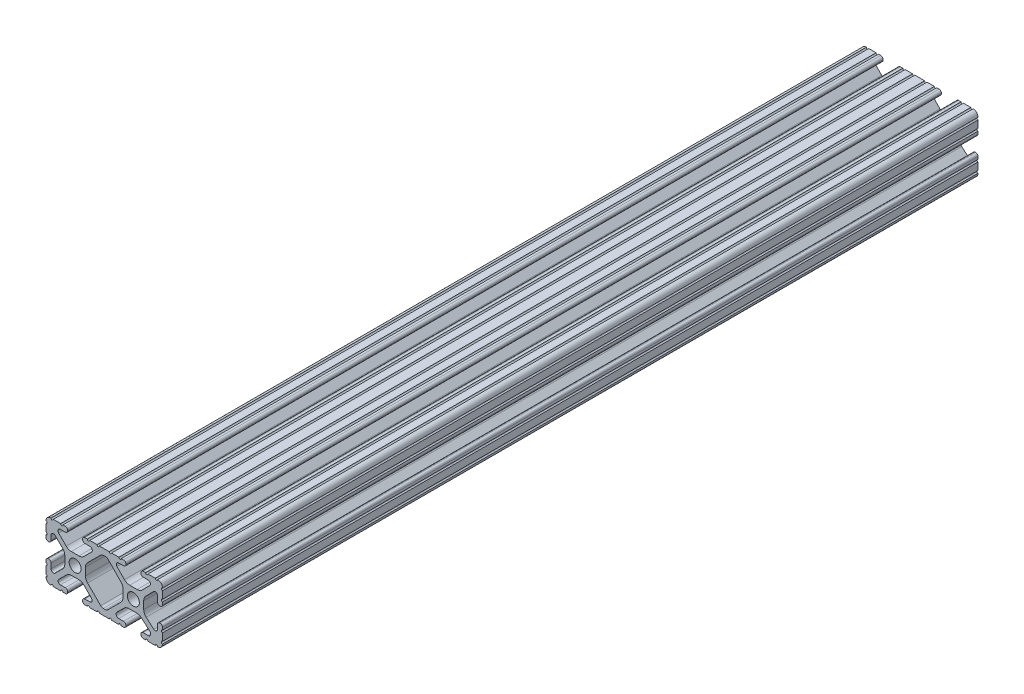
SolidWorks part; units mm, degrees
ref_plane "Front Plane" through (0, 0, 0) normal (0, 0, 1) x (1, 0, 0)
ref_plane "Top Plane" through (0, 0, 0) normal (0, 1, 0) x (1, 0, 0)
ref_plane "Right Plane" through (0, 0, 0) normal (1, 0, 0) x (0, 0, -1)
sketch "Sketch1" plane through (0, 0, 0) normal (0, 0, 1) x (1, 0, 0)
  line L0 (-7.2595, -3.8694) -> (-1.5457, -9.5728)
  line L1 (-8.1915, 1.6223) -> (-8.1915, -1.6223)
  line L2 (-1.504, 9.5765) -> (-7.252, 3.8768)
  line L3 (0.5515, 10.033) -> (-0.3952, 10.033)
  line L4 (7.2829, 3.8459) -> (1.6756, 9.5611)
  line L5 (8.1915, -1.6223) -> (8.1915, 1.6223)
  line L6 (1.5457, -9.5728) -> (7.2595, -3.8694)
  line L7 (-0.4332, -10.033) -> (0.4332, -10.033)
  line L8 (18.0171, 12.7) -> (16.9875, 12.7)
  line L9 (15.9385, 11.651) -> (15.9385, 11.5392)
  line L10 (16.9875, 10.4902) -> (19.1164, 10.4902)
  line L11 (19.8441, 8.7652) -> (16.619, 5.4551)
  line L12 (14.3449, 4.4958) -> (11.0833, 4.4958)
  line L13 (8.817, 5.4472) -> (5.5642, 8.7627)
  line L14 (6.2894, 10.4902) -> (8.4125, 10.4902)
  line L15 (9.4615, 11.5392) -> (9.4615, 11.651)
  line L16 (8.4125, 12.7) -> (7.3829, 12.7)
  line L17 (6.3669, 12.7) -> (3.1496, 12.7)
  line L18 (2.1336, 12.7) -> (-2.1336, 12.7)
  line L19 (-3.1496, 12.7) -> (-6.3669, 12.7)
  line L20 (-7.3829, 12.7) -> (-8.4125, 12.7)
  line L21 (-9.4615, 11.651) -> (-9.4615, 11.5392)
  line L22 (-8.4125, 10.4902) -> (-6.2836, 10.4902)
  line L23 (-5.5326, 8.6661) -> (-8.81, 5.4163)
  line L24 (-11.0455, 4.4958) -> (-14.3545, 4.4958)
  line L25 (-16.59, 5.4163) -> (-19.8674, 8.6661)
  line L26 (-19.1164, 10.4902) -> (-16.9875, 10.4902)
  line L27 (-15.9385, 11.5392) -> (-15.9385, 11.651)
  line L28 (-16.9875, 12.7) -> (-18.0171, 12.7)
  line L29 (-19.0331, 12.7) -> (-22.2504, 12.7)
  line L30 (-25.4, 9.5504) -> (-25.4, 6.3331)
  line L31 (-25.4, 5.3171) -> (-25.4, 4.2375)
  line L32 (-24.401, 3.2385) -> (-24.2392, 3.2385)
  line L33 (-23.1902, 4.2875) -> (-23.1902, 6.3347)
  line L34 (-21.434, 7.0665) -> (-18.148, 3.8082)
  line L35 (-17.2085, 1.5536) -> (-17.2085, -1.6952)
  line L36 (-18.1405, -3.9423) -> (-21.4316, -7.2274)
  line L37 (-23.1902, -6.498) -> (-23.1902, -4.2875)
  line L38 (-24.2392, -3.2385) -> (-24.351, -3.2385)
  line L39 (-25.4, -4.2875) -> (-25.4, -5.3171)
  line L40 (-25.4, -6.3331) -> (-25.4, -9.5504)
  line L41 (-22.2504, -12.7) -> (-19.0331, -12.7)
  line L42 (-18.0171, -12.7) -> (-16.9875, -12.7)
  line L43 (-15.9384, -11.651) -> (-15.9384, -11.5392)
  line L44 (-16.9875, -10.4902) -> (-19.1164, -10.4902)
  line L45 (-19.8341, -8.7551) -> (-16.4966, -5.4237)
  line L46 (-14.2536, -4.4958) -> (-11.1464, -4.4958)
  line L47 (-8.9034, -5.4237) -> (-5.5659, -8.7551)
  line L48 (-6.2836, -10.4902) -> (-8.4125, -10.4902)
  line L49 (-9.4616, -11.5392) -> (-9.4616, -11.651)
  line L50 (-8.4125, -12.7) -> (-7.3829, -12.7)
  line L51 (-6.3669, -12.7) -> (-3.1496, -12.7)
  line L52 (-2.1336, -12.7) -> (2.1336, -12.7)
  line L53 (3.1496, -12.7) -> (6.3669, -12.7)
  line L54 (7.3829, -12.7) -> (8.4125, -12.7)
  line L55 (9.4616, -11.651) -> (9.4616, -11.5392)
  line L56 (8.4125, -10.4902) -> (6.2894, -10.4902)
  line L57 (5.4807, -8.5353) -> (8.5979, -5.4237)
  line L58 (10.8409, -4.4958) -> (14.1026, -4.4958)
  line L59 (16.1879, -5.2766) -> (19.8682, -8.4822)
  line L60 (19.1164, -10.4902) -> (16.9875, -10.4902)
  line L61 (15.9384, -11.5392) -> (15.9384, -11.651)
  line L62 (16.9875, -12.7) -> (18.0171, -12.7)
  line L63 (19.0331, -12.7) -> (22.2504, -12.7)
  line L64 (25.4, -9.5504) -> (25.4, -6.3331)
  line L65 (25.4, -5.3171) -> (25.4, -4.2375)
  line L66 (24.401, -3.2385) -> (24.1892, -3.2385)
  line L67 (23.1902, -4.2375) -> (23.1902, -6.1559)
  line L68 (21.584, -6.8869) -> (18.2982, -4.025)
  line L69 (17.2085, -1.6308) -> (17.2085, 1.6308)
  line L70 (18.1094, 3.8465) -> (21.5263, 7.3534)
  line L71 (23.1902, 6.6769) -> (23.1902, 4.2375)
  line L72 (24.1892, 3.2385) -> (24.401, 3.2385)
  line L73 (25.4, 4.2375) -> (25.4, 5.3171)
  line L74 (25.4, 6.3332) -> (25.4, 9.5504)
  line L75 (22.2504, 12.7) -> (19.0331, 12.7)
  circle A0 centre (-12.7, 0) radius 2.6035
  circle A1 centre (12.7, 0) radius 2.6035
  arc A2 (-1.5457, -9.5728) -> (-0.4332, -10.033) centre (-0.4332, -8.4582) ccw
  arc A3 (-8.1915, -1.6223) -> (-7.2595, -3.8694) centre (-5.0165, -1.6223) ccw
  arc A4 (-7.252, 3.8768) -> (-8.1915, 1.6223) centre (-5.0165, 1.6223) ccw
  arc A5 (-0.3952, 10.033) -> (-1.504, 9.5765) centre (-0.3952, 8.4582) ccw
  arc A6 (1.6756, 9.5611) -> (0.5515, 10.033) centre (0.5515, 8.4582) ccw
  arc A7 (8.1915, 1.6223) -> (7.2829, 3.8459) centre (5.0165, 1.6223) ccw
  arc A8 (7.2595, -3.8694) -> (8.1915, -1.6223) centre (5.0165, -1.6223) ccw
  arc A9 (0.4332, -10.033) -> (1.5457, -9.5728) centre (0.4332, -8.4582) ccw
  arc A10 (18.0171, 12.7) -> (19.0331, 12.7) centre (18.5251, 12.7) ccw
  arc A11 (16.9875, 12.7) -> (15.9385, 11.651) centre (16.9875, 11.651) ccw
  arc A12 (15.9385, 11.5392) -> (16.9875, 10.4902) centre (16.9875, 11.5392) ccw
  arc A13 (19.8441, 8.7652) -> (19.1164, 10.4902) centre (19.1164, 9.4742) ccw
  arc A14 (14.3449, 4.4958) -> (16.619, 5.4551) centre (14.3449, 7.6708) ccw
  arc A15 (8.817, 5.4472) -> (11.0833, 4.4958) centre (11.0833, 7.6708) ccw
  arc A16 (6.2894, 10.4902) -> (5.5642, 8.7627) centre (6.2894, 9.4742) ccw
  arc A17 (8.4125, 10.4902) -> (9.4615, 11.5392) centre (8.4125, 11.5392) ccw
  arc A18 (9.4615, 11.651) -> (8.4125, 12.7) centre (8.4125, 11.651) ccw
  arc A19 (6.3669, 12.7) -> (7.3829, 12.7) centre (6.8749, 12.7) ccw
  arc A20 (2.1336, 12.7) -> (3.1496, 12.7) centre (2.6416, 12.7) ccw
  arc A21 (-3.1496, 12.7) -> (-2.1336, 12.7) centre (-2.6416, 12.7) ccw
  arc A22 (-7.3829, 12.7) -> (-6.3669, 12.7) centre (-6.8749, 12.7) ccw
  arc A23 (-8.4125, 12.7) -> (-9.4615, 11.651) centre (-8.4125, 11.651) ccw
  arc A24 (-9.4615, 11.5392) -> (-8.4125, 10.4902) centre (-8.4125, 11.5392) ccw
  arc A25 (-5.5326, 8.6661) -> (-6.2836, 10.4902) centre (-6.2836, 9.4235) ccw
  arc A26 (-11.0455, 4.4958) -> (-8.81, 5.4163) centre (-11.0455, 7.6708) ccw
  arc A27 (-16.59, 5.4163) -> (-14.3545, 4.4958) centre (-14.3545, 7.6708) ccw
  arc A28 (-19.1164, 10.4902) -> (-19.8674, 8.6661) centre (-19.1164, 9.4235) ccw
  arc A29 (-16.9875, 10.4902) -> (-15.9385, 11.5392) centre (-16.9875, 11.5392) ccw
  arc A30 (-15.9385, 11.651) -> (-16.9875, 12.7) centre (-16.9875, 11.651) ccw
  arc A31 (-19.0331, 12.7) -> (-18.0171, 12.7) centre (-18.5251, 12.7) ccw
  arc A32 (-23.2664, 12.6998) -> (-22.2504, 12.7) centre (-22.7584, 12.7) ccw
  arc A33 (-23.2664, 12.6998) -> (-25.3998, 10.5664) centre (-23.2918, 10.5918) ccw
  arc A34 (-25.4, 9.5504) -> (-25.3998, 10.5664) centre (-25.4, 10.0584) ccw
  arc A35 (-25.4, 5.3171) -> (-25.4, 6.3331) centre (-25.4, 5.8251) ccw
  arc A36 (-25.4, 4.2375) -> (-24.401, 3.2385) centre (-24.401, 4.2375) ccw
  arc A37 (-24.2392, 3.2385) -> (-23.1902, 4.2875) centre (-24.2392, 4.2875) ccw
  arc A38 (-21.434, 7.0665) -> (-23.1902, 6.3347) centre (-22.1596, 6.3347) ccw
  arc A39 (-17.2085, 1.5536) -> (-18.148, 3.8082) centre (-20.3835, 1.5536) ccw
  arc A40 (-18.1405, -3.9423) -> (-17.2085, -1.6952) centre (-20.3835, -1.6952) ccw
  arc A41 (-23.1902, -6.498) -> (-21.4316, -7.2274) centre (-22.1596, -6.498) ccw
  arc A42 (-23.1902, -4.2875) -> (-24.2392, -3.2385) centre (-24.2392, -4.2875) ccw
  arc A43 (-24.351, -3.2385) -> (-25.4, -4.2875) centre (-24.351, -4.2875) ccw
  arc A44 (-25.4, -6.3331) -> (-25.4, -5.3171) centre (-25.4, -5.8251) ccw
  arc A45 (-25.3998, -10.5664) -> (-25.4, -9.5504) centre (-25.4, -10.0584) ccw
  arc A46 (-25.3998, -10.5664) -> (-23.2664, -12.6998) centre (-23.2918, -10.5918) ccw
  arc A47 (-22.2504, -12.7) -> (-23.2664, -12.6998) centre (-22.7584, -12.7) ccw
  arc A48 (-18.0171, -12.7) -> (-19.0331, -12.7) centre (-18.5251, -12.7) ccw
  arc A49 (-16.9875, -12.7) -> (-15.9384, -11.651) centre (-16.9875, -11.651) ccw
  arc A50 (-15.9384, -11.5392) -> (-16.9875, -10.4902) centre (-16.9875, -11.5392) ccw
  arc A51 (-19.8341, -8.7551) -> (-19.1164, -10.4902) centre (-19.1164, -9.4742) ccw
  arc A52 (-14.2536, -4.4958) -> (-16.4966, -5.4237) centre (-14.2536, -7.6708) ccw
  arc A53 (-8.9034, -5.4237) -> (-11.1464, -4.4958) centre (-11.1464, -7.6708) ccw
  arc A54 (-6.2836, -10.4902) -> (-5.5659, -8.7551) centre (-6.2836, -9.4742) ccw
  arc A55 (-8.4125, -10.4902) -> (-9.4616, -11.5392) centre (-8.4125, -11.5392) ccw
  arc A56 (-9.4616, -11.651) -> (-8.4125, -12.7) centre (-8.4125, -11.651) ccw
  arc A57 (-6.3669, -12.7) -> (-7.3829, -12.7) centre (-6.8749, -12.7) ccw
  arc A58 (-2.1336, -12.7) -> (-3.1496, -12.7) centre (-2.6416, -12.7) ccw
  arc A59 (3.1496, -12.7) -> (2.1336, -12.7) centre (2.6416, -12.7) ccw
  arc A60 (7.3829, -12.7) -> (6.3669, -12.7) centre (6.8749, -12.7) ccw
  arc A61 (8.4125, -12.7) -> (9.4616, -11.651) centre (8.4125, -11.651) ccw
  arc A62 (9.4616, -11.5392) -> (8.4125, -10.4902) centre (8.4125, -11.5392) ccw
  arc A63 (5.4807, -8.5353) -> (6.2894, -10.4902) centre (6.2894, -9.3455) ccw
  arc A64 (10.8409, -4.4958) -> (8.5979, -5.4237) centre (10.8409, -7.6708) ccw
  arc A65 (16.1879, -5.2766) -> (14.1026, -4.4958) centre (14.1026, -7.6708) ccw
  arc A66 (19.1164, -10.4902) -> (19.8682, -8.4822) centre (19.1164, -9.3455) ccw
  arc A67 (16.9875, -10.4902) -> (15.9384, -11.5392) centre (16.9875, -11.5392) ccw
  arc A68 (15.9384, -11.651) -> (16.9875, -12.7) centre (16.9875, -11.651) ccw
  arc A69 (19.0331, -12.7) -> (18.0171, -12.7) centre (18.5251, -12.7) ccw
  arc A70 (23.2664, -12.6998) -> (22.2504, -12.7) centre (22.7584, -12.7) ccw
  arc A71 (23.2664, -12.6998) -> (25.3998, -10.5664) centre (23.2918, -10.5918) ccw
  arc A72 (25.4, -9.5504) -> (25.3998, -10.5664) centre (25.4, -10.0584) ccw
  arc A73 (25.4, -5.3171) -> (25.4, -6.3331) centre (25.4, -5.8251) ccw
  arc A74 (25.4, -4.2375) -> (24.401, -3.2385) centre (24.401, -4.2375) ccw
  arc A75 (24.1892, -3.2385) -> (23.1902, -4.2375) centre (24.1892, -4.2375) ccw
  arc A76 (21.584, -6.8869) -> (23.1902, -6.1559) centre (22.2207, -6.1559) ccw
  arc A77 (17.2085, -1.6308) -> (18.2982, -4.025) centre (20.3835, -1.6308) ccw
  arc A78 (18.1094, 3.8465) -> (17.2085, 1.6308) centre (20.3835, 1.6308) ccw
  arc A79 (23.1902, 6.6769) -> (21.5263, 7.3534) centre (22.2207, 6.6769) ccw
  arc A80 (23.1902, 4.2375) -> (24.1892, 3.2385) centre (24.1892, 4.2375) ccw
  arc A81 (24.401, 3.2385) -> (25.4, 4.2375) centre (24.401, 4.2375) ccw
  arc A82 (25.4, 6.3332) -> (25.4, 5.3171) centre (25.4, 5.8251) ccw
  arc A83 (25.3998, 10.5664) -> (25.4, 9.5504) centre (25.4, 10.0584) ccw
  arc A84 (25.3998, 10.5664) -> (23.2664, 12.6998) centre (23.2918, 10.5918) ccw
  arc A85 (22.2504, 12.7) -> (23.2664, 12.6998) centre (22.7584, 12.7) ccw
  point P248 (0, 10.033)
extrude "Boss-Extrude1" add sketch "Sketch1" along normal mid plane 355.6
